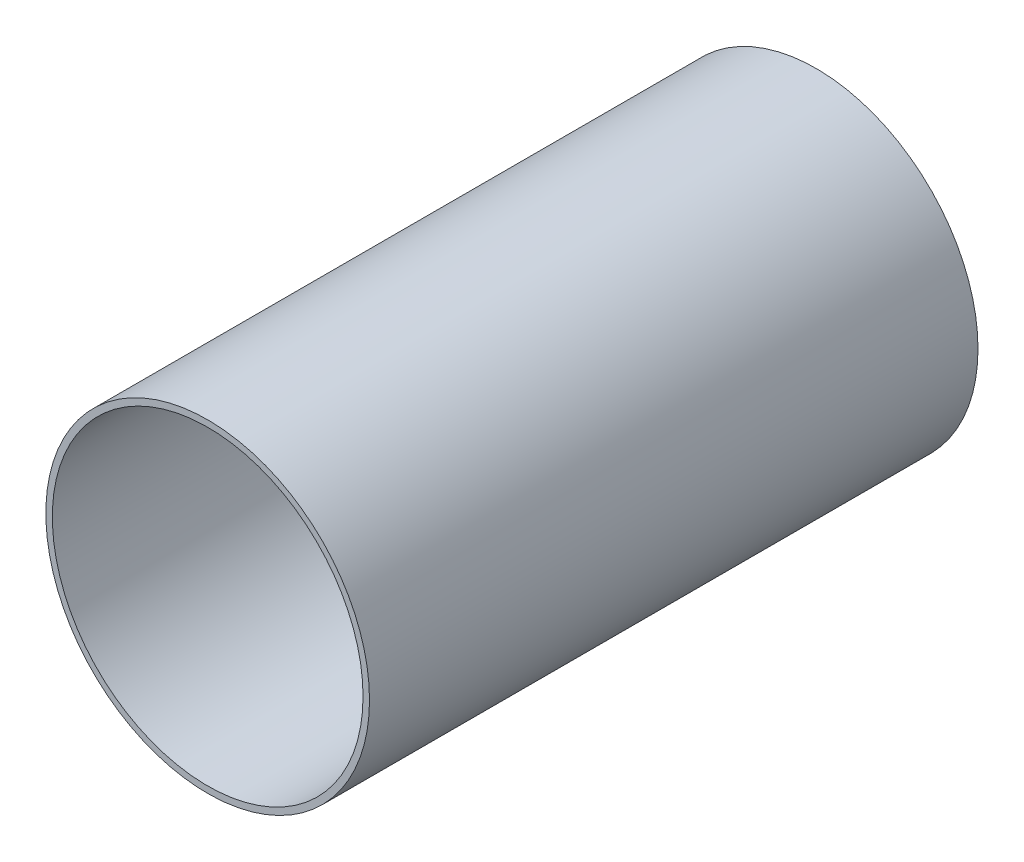
SolidWorks part; units mm, degrees
material "Acrylic (Medium-high impact)"
ref_plane "Front" through (0, 0, 0) normal (0, 0, 1) x (1, 0, 0)
ref_plane "Top" through (0, 0, 0) normal (0, 1, 0) x (1, 0, 0)
ref_plane "Right" through (0, 0, 0) normal (1, 0, 0) x (0, 0, -1)
sketch "Sketch2" plane through (0, 0, 0) normal (0, 0, 1) x (1, 0, 0)
  circle A0 centre (0, 0) radius 79.375
  dimension "D1" = 158.75
extrude "Boss-Extrude1" add sketch "Sketch2" along normal blind 298.45
sketch "Sketch3" plane through (0, 0, 298.45) normal (0, 0, 1) x (1, 0, 0)
  circle A0 centre (0, 0) radius 76.2
  dimension "D1" = 152.4
extrude "Cut-Extrude1" cut sketch "Sketch3" against normal blind 298.45
